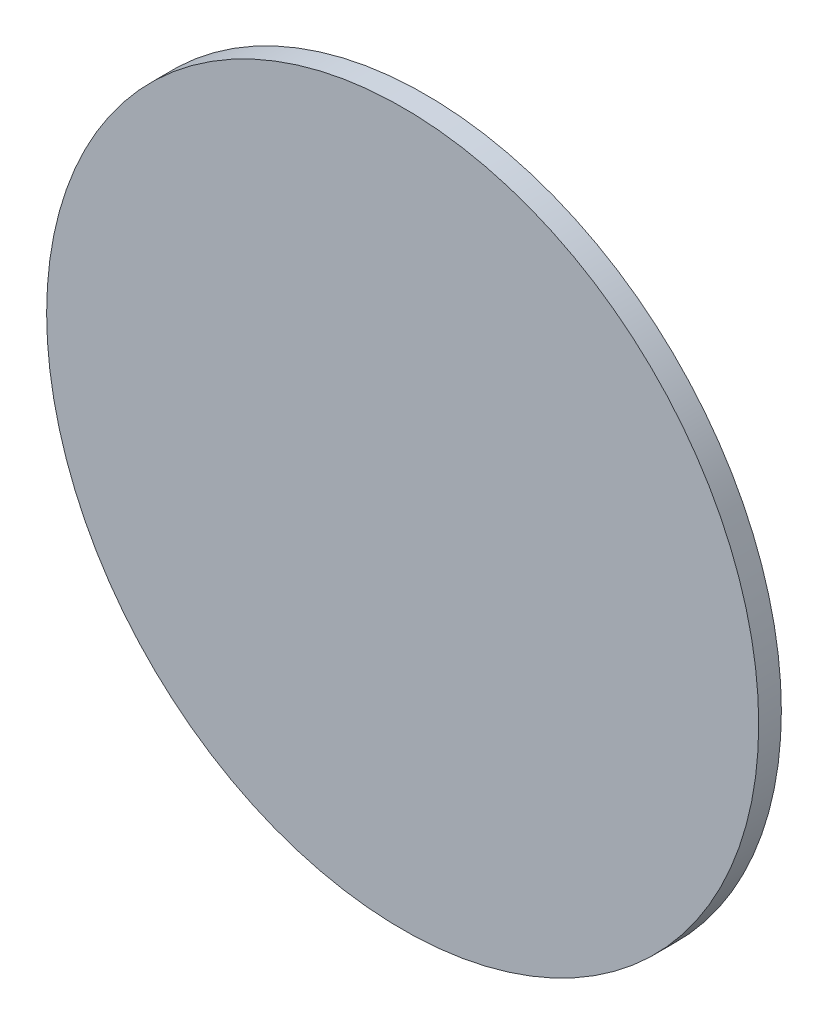
SolidWorks part; units mm, degrees
material "ABS PC"
ref_plane "Front Plane" through (0, 0, 0) normal (0, 0, 1) x (1, 0, 0)
ref_plane "Top Plane" through (0, 0, 0) normal (0, 1, 0) x (1, 0, 0)
ref_plane "Right Plane" through (0, 0, 0) normal (1, 0, 0) x (0, 0, -1)
sketch "Sketch1" plane through (0, 0, 0) normal (0, 0, 1) x (1, 0, 0)
  circle A0 centre (0, 0) radius 24.9555
  circle A1 centre (0, 0) radius 25.3365 construction
  dimension "D1" = 0.381
extrude "Boss-Extrude1" add sketch "Sketch1" along normal blind 1.5875
